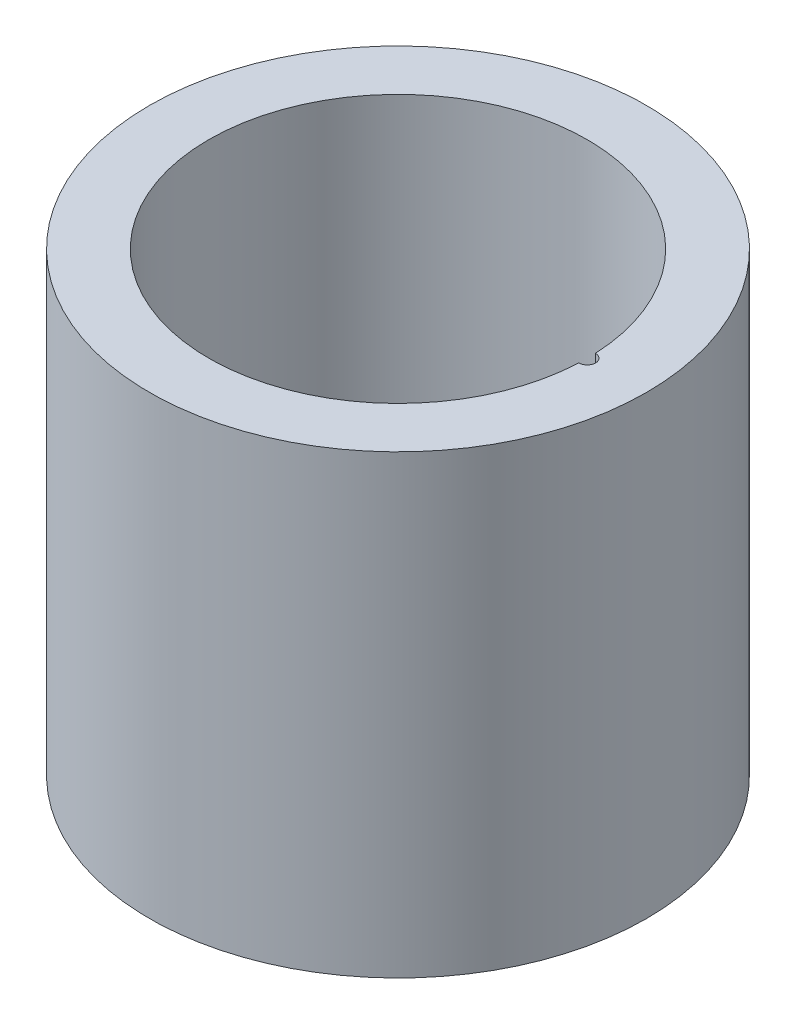
SolidWorks part; units mm, degrees
ref_plane "Front Plane" through (0, 0, 0) normal (0, 0, 1) x (1, 0, 0)
ref_plane "Top Plane" through (0, 0, 0) normal (0, 1, 0) x (1, 0, 0)
ref_plane "Right Plane" through (0, 0, 0) normal (1, 0, 0) x (0, 0, -1)
sketch "Sketch4" plane through (0, 0, 0) normal (0, 0, 1) x (1, 0, 0)
  line L0 (0, -1100.0337) -> (0, 53901.6512) construction
  line L1 (0, 0) -> (30, 0)
  line L2 (30, 0) -> (30, 55)
  line L3 (30, 55) -> (22.8477, 55)
  line L4 (22.8477, 55) -> (22.8477, 15)
  line L5 (22.8477, 10) -> (22.8477, 5)
  line L6 (22.8477, 5) -> (0, 5)
  line L7 (22.8477, 10) -> (23.8477, 10)
  line L8 (23.8477, 10) -> (23.8477, 15)
  line L9 (23.8477, 15) -> (22.8477, 15)
  line L10 (0, 5) -> (0, 0)
  dimension "D1" = 30
  dimension "D2" = 55
  dimension "D3" = 5
  dimension "D4" = 7.1523
  dimension "D5" = 5
  dimension "D6" = 5
  dimension "D7" = 1
revolve "Revolve2" add sketch "Sketch4" angle 360 about L0
sketch "Sketch6" plane through (0, 55, 0) normal (0, 1, 0) x (1, 0, 0)
  circle A0 centre (22.8477, 0) radius 1
  circle A1 centre (0, 0) radius 22.8477 construction
  circle A2 centre (0, 0) radius 22.8477 construction
  dimension "D1" = 2
extrude "Cut-Extrude4" cut sketch "Sketch6" against normal blind 40
